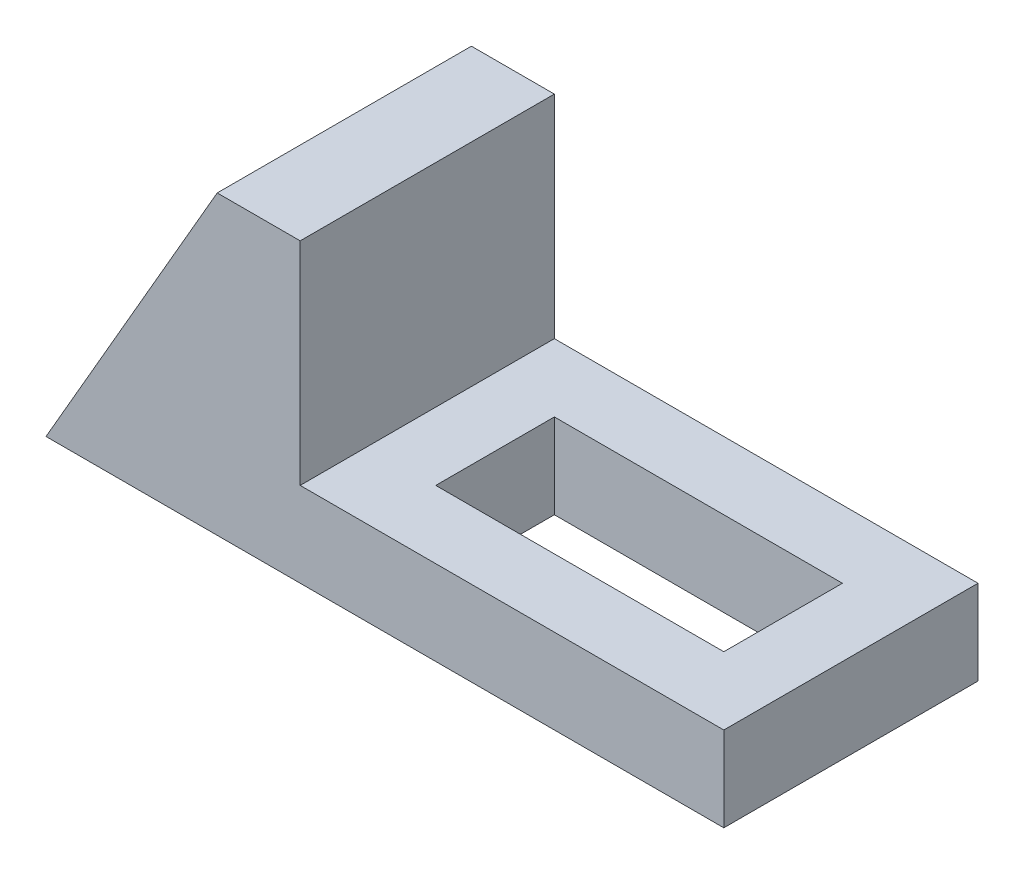
SolidWorks part; units mm, degrees
ref_plane "Front Plane" through (0, 0, 0) normal (0, 0, 1) x (1, 0, 0)
ref_plane "Top Plane" through (0, 0, 0) normal (0, 1, 0) x (1, 0, 0)
ref_plane "Right Plane" through (0, 0, 0) normal (1, 0, 0) x (0, 0, -1)
sketch "Sketch1" plane through (0, 0, 0) normal (0, 0, 1) x (1, 0, 0)
  line L0 (0, 0) -> (20.2073, 35)
  line L1 (20.2073, 35) -> (30, 35)
  line L2 (30, 35) -> (30, 10)
  line L3 (30, 10) -> (80, 10)
  line L4 (80, 10) -> (80, 0)
  line L5 (80, 0) -> (0, 0)
  dimension "D1" = 60
  dimension "D2" = 35
  dimension "D3" = 30
  dimension "D4" = 80
  dimension "D5" = 10
extrude "Boss-Extrude1" add sketch "Sketch1" along normal blind 30
sketch "Sketch2" plane through (0, 10, 0) normal (0, 1, 0) x (1, 0, 0)
  line L0 (80, 0) -> (30, 0) construction
  line L1 (38, -8) -> (72, -8)
  line L2 (38, -8) -> (38, -22)
  line L3 (38, -22) -> (72, -22)
  line L4 (72, -8) -> (72, -22)
  line L5 (80, -30) -> (80, 0) construction
  line L6 (80, -30) -> (30, -30) construction
  line L7 (30, -30) -> (30, 0) construction
  dimension "D1" = 8
  dimension "D2" = 8
  dimension "D3" = 8
  dimension "D4" = 8
extrude "Cut-Extrude1" cut sketch "Sketch2" against normal blind 30
